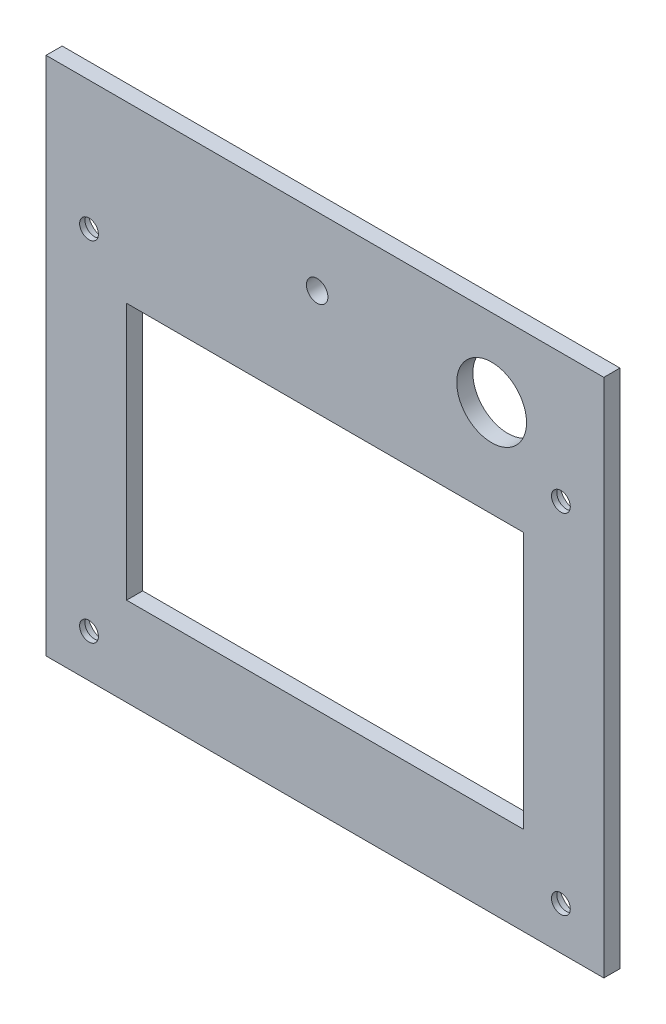
SolidWorks part; units mm, degrees
ref_plane "Front Plane" through (0, 0, 0) normal (0, 0, 1) x (1, 0, 0)
ref_plane "Top Plane" through (0, 0, 0) normal (0, 1, 0) x (1, 0, 0)
ref_plane "Right Plane" through (0, 0, 0) normal (1, 0, 0) x (0, 0, -1)
sketch "Sketch1" plane through (0, 0, 0) normal (0, 0, 1) x (1, 0, 0)
  line L0 (5, 8.5) -> (5, 56.4)
  line L1 (0, 0) -> (87.9, 0) construction
  line L2 (0, 0) -> (0, 64.9) construction
  line L3 (0, 64.9) -> (87.9, 64.9) construction
  line L4 (87.9, 0) -> (87.9, 64.9) construction
  line L6 (82.9, 8.5) -> (82.9, 56.4)
  line L8 (-5, -5) -> (-5, 69.9)
  line L10 (92.9, -5) -> (92.9, 69.9)
  line L11 (-5, -5) -> (92.9, -5)
  line L12 (5, 5) -> (5, 59.9) construction
  line L13 (82.9, 8.5) -> (5, 8.5)
  line L15 (82.9, 56.4) -> (5, 56.4)
  line L16 (82.9, 5) -> (82.9, 59.9) construction
  line L17 (5, 5) -> (82.9, 5) construction
  line L18 (5, 59.9) -> (82.9, 59.9) construction
  line L19 (-5, 69.9) -> (92.9, 69.9) construction
  line L21 (-5, 69.9) -> (-5, 85.9)
  line L22 (-5, 85.9) -> (92.9, 85.9)
  line L23 (92.9, 69.9) -> (92.9, 85.9)
  circle A0 centre (0, 64.9) radius 1.75
  circle A1 centre (87.9, 64.9) radius 1.75
  circle A2 centre (87.9, 0) radius 1.75
  circle A3 centre (0, 0) radius 1.75
  circle A4 centre (75, 74.4) radius 6.5
  circle A5 centre (42.5, 76.15) radius 2
  dimension "D5" = 3.5
  dimension "D6" = 3.5
  dimension "D7" = 3.5
  dimension "D8" = 3.5
  dimension "D10" = 13
  dimension "D14" = 4
  dimension "D1" = 64.9
  dimension "D2" = 87.9
  dimension "D9" = 16
  dimension "D11" = 80
  dimension "D12" = 11.5
  dimension "D13" = 9.75
  dimension "D15" = 47.5
  dimension "D3" = 5
  dimension "D4" = 5
extrude "Boss-Extrude1" add sketch "Sketch1" along normal blind 3
sketch "Sketch2" plane through (0, 0, 3) normal (0, 0, 1) x (1, 0, 0)
  line L0 (82.9, 56.4) -> (5, 56.4) construction
  line L1 (82.9, 8.5) -> (80.9, 8.5)
  line L2 (82.9, 8.5) -> (82.9, 56.4)
  line L3 (82.9, 56.4) -> (80.9, 56.4)
  line L4 (80.9, 8.5) -> (80.9, 56.4)
  line L6 (5, 8.5) -> (7, 8.5)
  line L7 (5, 8.5) -> (5, 56.4)
  line L8 (5, 56.4) -> (7, 56.4)
  line L9 (7, 8.5) -> (7, 56.4)
  dimension "D1" = 2
  dimension "D2" = 2
extrude "Boss-Extrude2" add sketch "Sketch2" against normal up to surface (3 mm away) up to face at (1.75, 0, 0)
sketch "Sketch3" plane through (0, 0, 0) normal (0, 0, -1) x (-1, 0, 0)
  line L5 (5, 85) -> (-92.9, 85)
  line L6 (5, 85) -> (5, 69.9)
  line L7 (5, 69.9) -> (-92.9, 69.9)
  line L8 (-92.9, 85) -> (-92.9, 69.9)
  circle A0 centre (-72.73, 77.45) radius 5.5
  dimension "D2" = 11
  dimension "D1" = 7.55
  dimension "D3" = 15.1
extrude "Boss-Extrude3" [suppressed] add sketch "Sketch3" against normal up to surface (5 mm away)
sketch "Sketch4" plane through (92.9, 0, 0) normal (1, 0, 0) x (0, 0, -1)
  line L1 (0, -5) -> (-15, -5)
  line L2 (0, -5) -> (0, 87.7387)
  line L3 (0, 87.7387) -> (-15, 87.7387)
  line L4 (-15, -5) -> (-15, 87.7387)
  dimension "D1" = 15
extrude "Boss-Extrude4" add sketch "Sketch4" along normal blind 3
sketch "Sketch5" plane through (-5, 0, 0) normal (-1, 0, 0) x (0, 0, 1)
  line L1 (0, -5) -> (15, -5)
  line L2 (0, -5) -> (0, 87.0139)
  line L3 (0, 87.0139) -> (15, 87.0139)
  line L4 (15, -5) -> (15, 87.0139)
  dimension "D1" = 15
extrude "Boss-Extrude5" add sketch "Sketch5" along normal blind 3
sketch "Sketch7" plane through (0, -5, 0) normal (0, -1, 0) x (-1, 0, 0)
  line L1 (-95.9, 0) -> (8, 0)
  line L2 (-95.9, 0) -> (-95.9, -15)
  line L3 (-95.9, -15) -> (8, -15)
  line L4 (8, 0) -> (8, -15)
extrude "Boss-Extrude6" add sketch "Sketch7" along normal blind 3
sketch "Sketch8" [suppressed] plane through (0, 85, 0) normal (0, 1, 0) x (1, 0, 0)
  line L1 (-8, -15) -> (95.9, -15)
  line L2 (-8, -15) -> (-8, 0)
  line L3 (-8, 0) -> (95.9, 0)
  line L4 (95.9, -15) -> (95.9, 0)
extrude "Boss-Extrude7" [suppressed] add sketch "Sketch8" along normal blind 3
sketch "Sketch9" plane through (0, 0, 0) normal (0, 0, -1) x (-1, 0, 0)
  circle A0 centre (0, 0) radius 3.25
  circle A1 centre (-87.9, 0) radius 3.25
  circle A2 centre (-87.9, 64.9) radius 3.25
  circle A3 centre (0, 64.9) radius 3.25
  dimension "D1" = 6.5
  dimension "D2" = 6.5
  dimension "D3" = 6.5
  dimension "D4" = 6.5
extrude "Cut-Extrude1" cut sketch "Sketch9" against normal blind 2
sketch "Sketch10" plane through (0, 85.9, 0) normal (0, 1, 0) x (1, 0, 0)
  line L1 (95.9, -15) -> (-8, -15)
  line L2 (95.9, -15) -> (95.9, 0)
  line L3 (95.9, 0) -> (-8, 0)
  line L4 (-8, -15) -> (-8, 0)
extrude "Boss-Extrude8" add sketch "Sketch10" along normal blind 3
sketch "Sketch12" plane through (0, 0, 3) normal (0, 0, 1) x (1, 0, 0)
  circle A0 centre (0, 64.9) radius 1.75
  circle A1 centre (0, 64.9) radius 3.75
  circle A2 centre (87.9, 64.9) radius 1.75
  circle A3 centre (87.9, 0) radius 1.75
  circle A4 centre (0, 0) radius 1.75
  circle A5 centre (0, 0) radius 3.75
  circle A6 centre (87.9, 64.9) radius 3.75
  circle A7 centre (87.9, 0) radius 3.75
  dimension "D1" = 2
  dimension "D2" = 3.5
  dimension "D3" = 3.5
  dimension "D4" = 3.5
  dimension "D5" = 2
extrude "Boss-Extrude9" add sketch "Sketch12" along normal blind 8
sketch "Sketch13" plane through (95.9, 0, 0) normal (1, 0, 0) x (0, 0, -1)
  line L0 (-15, 88.9) -> (-15, -8) construction
  line L1 (-15, 65.0469) -> (-12, 65.0469)
  line L2 (-15, 65.0469) -> (-15, 42.0469)
  line L3 (-15, 42.0469) -> (-12, 42.0469)
  line L4 (-12, 65.0469) -> (-12, 42.0469)
  line L5 (-15, 88.9) -> (0, 88.9) construction
  dimension "D1" = 23
  dimension "D2" = 3
  dimension "D3" = 23.8531
extrude "Cut-Extrude2" cut sketch "Sketch13" against normal blind 8
sketch "Sketch14" plane through (0, 0, 15) normal (0, 0, 1) x (1, 0, 0)
  line L1 (235.8002, -50.1835) -> (-45.7554, -50.1835)
  line L2 (235.8002, -50.1835) -> (235.8002, 123.5534)
  line L3 (235.8002, 123.5534) -> (-45.7554, 123.5534)
  line L4 (-45.7554, -50.1835) -> (-45.7554, 123.5534)
  line L5 (235.8002, -50.1835) -> (-45.7554, 123.5534) construction
  line L6 (235.8002, 123.5534) -> (-45.7554, -50.1835) construction
extrude "Cut-Extrude3" cut sketch "Sketch14" against normal up to surface (12 mm away) up to face at (91.65, 64.9, 3)
